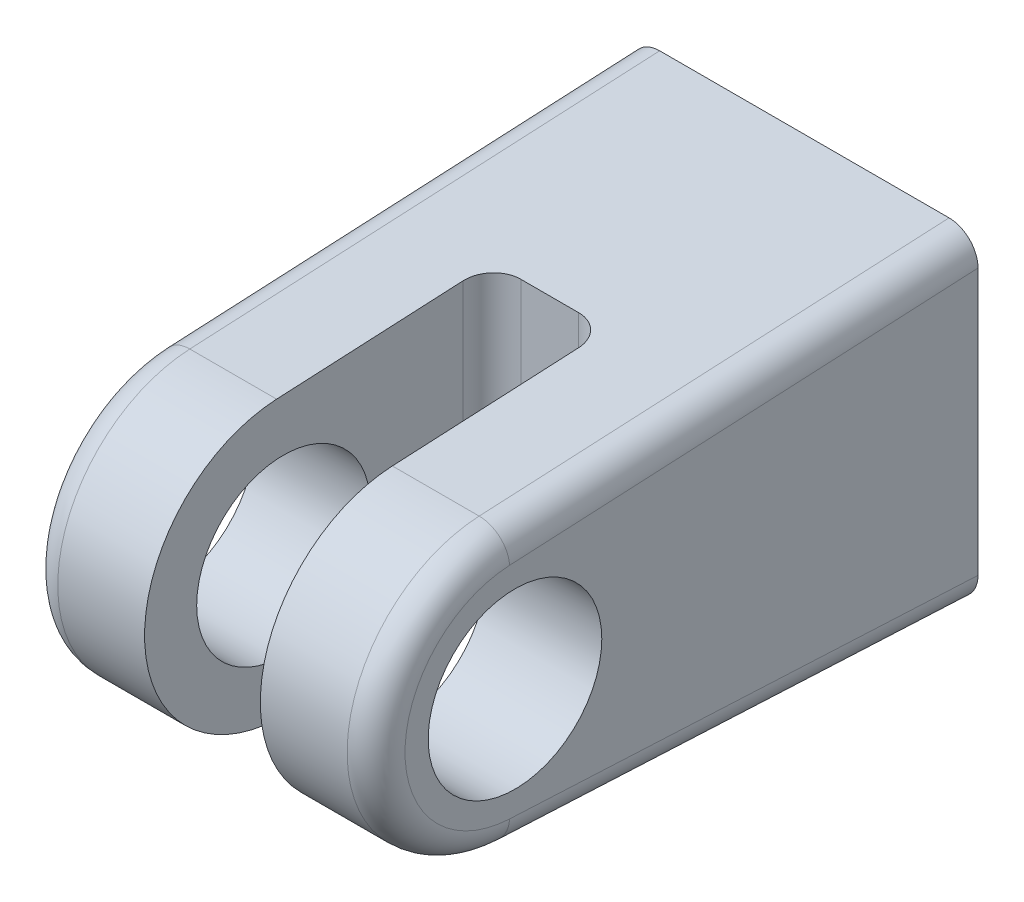
SolidWorks part; units mm, degrees
material "Plain Carbon Steel"
ref_plane "Front" through (0, 0, 0) normal (0, 0, 1) x (1, 0, 0)
ref_plane "Top" through (0, 0, 0) normal (0, 1, 0) x (1, 0, 0)
ref_plane "Right" through (0, 0, 0) normal (1, 0, 0) x (0, 0, -1)
sketch "Sketch2" plane through (0, 0, 0) normal (1, 0, 0) x (0, 0, -1)
  line L0 (0, 8.89) -> (-25.7777, 7.6106)
  line L1 (0, -8.89) -> (-25.7777, -7.6106)
  line L2 (0, 8.89) -> (0, -8.89)
  line L3 (0, 0) -> (-66.2459, 0) construction
  arc A0 (-25.7777, 7.6106) -> (-25.7777, -7.6106) centre (-25.4, 0) ccw
  dimension "D1" = 7.62
  dimension "D2" = 17.78
  dimension "D3" = 25.4
extrude "Extrude2" add sketch "Sketch2" along normal mid plane 19.05
sketch "Sketch3" plane through (0, 0, 0) normal (0, 1, 0) x (1, 0, 0)
  line L0 (0, -13.97) -> (0, 0) construction
  line L1 (-3.175, -13.97) -> (3.175, -13.97)
  line L2 (-3.175, -13.97) -> (-3.175, -33.02)
  line L3 (-3.175, -33.02) -> (3.175, -33.02)
  line L4 (3.175, -13.97) -> (3.175, -33.02)
  line L5 (-9.525, -33.02) -> (9.525, -33.02) construction
  dimension "D1" = 6.35
  dimension "D2" = 19.05
extrude "Cut-Extrude1" cut sketch "Sketch3" against normal through all and the other way through all
sketch "Sketch4" plane through (9.525, 0, 0) normal (1, 0, 0) x (0, 0, -1)
  circle A0 centre (-25.4, 0) radius 4.7625
  dimension "D1" = 9.525
extrude "Cut-Extrude2" cut sketch "Sketch4" against normal through all
sketch "Sketch5" plane through (0, 0, 0) normal (0, 0, -1) x (-1, 0, 0)
  circle A0 centre (0, 0) radius 6.35
  dimension "D1" = 12.7
extrude "Cut-Extrude3" cut sketch "Sketch5" against normal blind 9.525
fillet "Fillet1" radius 1.5875 8 edges at (-9.525, -8.2503, 12.8889) (-9.525, 0, 33.02) (9.525, -8.2503, 12.8889) (9.525, 0, 33.02) (-9.525, 8.2503, 12.8889) (9.525, 8.2503, 12.8889) (-3.175, 0, 13.97) (3.175, 0, 13.97)
